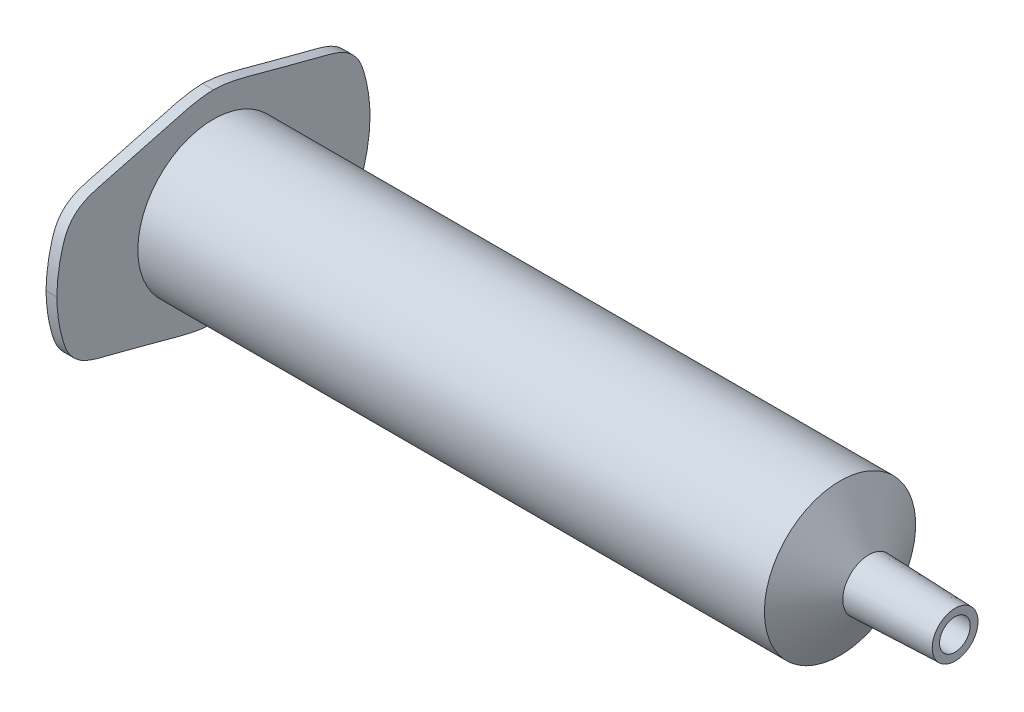
SolidWorks part; units mm, degrees
material "Акрил (Средняя-высокая ударопрочность)"
ref_plane "Спереди" through (0, 0, 0) normal (0, 0, 1) x (1, 0, 0)
ref_plane "Сверху" through (0, 0, 0) normal (0, 1, 0) x (1, 0, 0)
ref_plane "Справа" through (0, 0, 0) normal (1, 0, 0) x (0, 0, -1)
other "Configuration Table"
sketch "Эскиз1" plane through (0, 0, 0) normal (0, 0, 1) x (1, 0, 0)
  line L0 (-41.3424, 7) -> (16.6576, 7)
  line L1 (16.6576, 7) -> (19.3134, 2.4)
  line L2 (19.3134, 2.4) -> (27.3134, 2.1206)
  line L3 (-11.5653, 0) -> (33.4539, 0) construction
  dimension "D1" = 7
  dimension "D2" = 58
  dimension "D3" = 120
  dimension "D4" = 122
  dimension "D5" = 8
  dimension "D6" = 2.4
revolve "Повернуть-Тонкостенный3" add sketch "Эскиз1" angle 360 about L3
sketch "Эскиз2" plane through (-41.3424, 0, 0) normal (-1, 0, 0) x (0, 0, 1)
  line L0 (14.5, 0) -> (-14.5, 0) construction
  circle A0 centre (0, 0) radius 6.3
  spline S0 degree 3 poles (-14.5, 0) (-14.4747, -1.2506) (-14.2423, -3.0181) (-13.4807, -5.1562) (-12.3869, -6.2421) (-11.1428, -6.7274) (-9.5624, -7.1252) (-7.4837, -7.6919) (-4.7244, -8.3637) (-2.267, -9.1224) (-0.6552, -9.3328) (-0.0828, -9.3557) (0, -9.3579) knots 0 0 0 0 0.17878 0.255445 0.319698 0.392573 0.443879 0.553726 0.701163 0.851191 0.921407 0.933286 0.933286 0.933286 0.933286
  spline S1 degree 3 poles (14.5, 0) (14.4747, -1.2506) (14.2423, -3.0181) (13.4807, -5.1562) (12.3869, -6.2421) (11.1428, -6.7274) (9.5624, -7.1252) (7.4837, -7.6919) (4.7244, -8.3637) (2.267, -9.1224) (0.6552, -9.3328) (0.0828, -9.3557) (0, -9.3579) knots 0 0 0 0 0.17878 0.255445 0.319698 0.392573 0.443879 0.553726 0.701163 0.851191 0.921407 0.933286 0.933286 0.933286 0.933286
  spline S2 degree 3 poles (14.5, 0) (14.4747, 1.2506) (14.2423, 3.0181) (13.4807, 5.1562) (12.3869, 6.2421) (11.1428, 6.7274) (9.5624, 7.1252) (7.4837, 7.6919) (4.7244, 8.3637) (2.267, 9.1224) (0.6552, 9.3328) (0.0828, 9.3557) (0, 9.3579) knots 0 0 0 0 0.17878 0.255445 0.319698 0.392573 0.443879 0.553726 0.701163 0.851191 0.921407 0.933286 0.933286 0.933286 0.933286
  spline S3 degree 3 poles (-14.5, 0) (-14.4747, 1.2506) (-14.2423, 3.0181) (-13.4807, 5.1562) (-12.3869, 6.2421) (-11.1428, 6.7274) (-9.5624, 7.1252) (-7.4837, 7.6919) (-4.7244, 8.3637) (-2.267, 9.1224) (-0.6552, 9.3328) (-0.0828, 9.3557) (0, 9.3579) knots 0 0 0 0 0.17878 0.255445 0.319698 0.392573 0.443879 0.553726 0.701163 0.851191 0.921407 0.933286 0.933286 0.933286 0.933286
extrude "Бобышка-Вытянуть1" add sketch "Эскиз2" along normal blind 1
sketch "Эскиз3" plane through (0, 0, 0) normal (0, 0, 1) x (1, 0, 0)
  line L0 (17.0462, -4.9269) -> (23.4267, 6.1244) construction
  line L1 (16.2535, -6.3) -> (18.9012, -1.714) construction
  line L2 (17.9639, 3.3375) -> (23.0191, -5.4184) construction
  line L3 (18.9012, 1.714) -> (16.2535, 6.3) construction
  line L4 (19.8908, 0) -> (-20.1092, 0)
  dimension "D1" = 40
